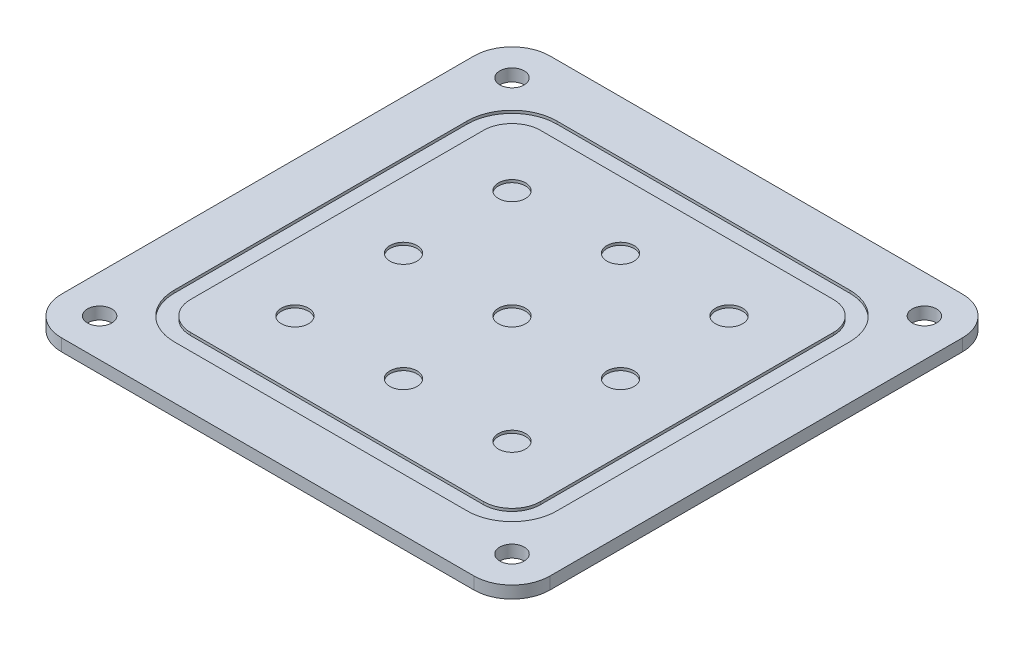
SolidWorks part; units mm, degrees
ref_plane "Front Plane" through (0, 0, 0) normal (0, 0, 1) x (1, 0, 0)
ref_plane "Top Plane" through (0, 0, 0) normal (0, 1, 0) x (1, 0, 0)
ref_plane "Right Plane" through (0, 0, 0) normal (1, 0, 0) x (0, 0, -1)
sketch "Sketch1" plane through (0, 0, 0) normal (0, 1, 0) x (1, 0, 0)
  line L1 (-45, -45) -> (45, -45)
  line L2 (-45, -45) -> (-45, 45)
  line L3 (-45, 45) -> (45, 45)
  line L4 (45, -45) -> (45, 45)
  line L5 (-45, -45) -> (45, 45) construction
  line L6 (-45, 45) -> (45, -45) construction
  point P0 (0, 0)
  dimension "D1" = 90
extrude "Boss-Extrude1" add sketch "Sketch1" along normal blind 2.25
sketch "Sketch2" plane through (0, 2.25, 0) normal (0, 1, 0) x (1, 0, 0)
  line L0 (-32.25, -27) -> (-32.25, 27)
  line L1 (-27, -35.25) -> (27, -35.25)
  line L2 (-35.25, -27) -> (-35.25, 27)
  line L3 (-27, 35.25) -> (27, 35.25)
  line L4 (35.25, -27) -> (35.25, 27)
  line L5 (0, 35.25) -> (0, -35.25) construction
  line L6 (-35.25, 0) -> (35.25, 0) construction
  line L7 (-27, 32.25) -> (27, 32.25)
  line L8 (32.25, -27) -> (32.25, 27)
  line L9 (-27, -32.25) -> (27, -32.25)
  arc A0 (-27, -35.25) -> (-35.25, -27) centre (-27, -27) cw
  arc A1 (27, -35.25) -> (35.25, -27) centre (27, -27) ccw
  arc A2 (27, 35.25) -> (35.25, 27) centre (27, 27) cw
  arc A3 (-35.25, 27) -> (-27, 35.25) centre (-27, 27) cw
  arc A4 (-32.25, 27) -> (-27, 32.25) centre (-27, 27) cw
  arc A5 (27, 32.25) -> (32.25, 27) centre (27, 27) cw
  arc A6 (27, -32.25) -> (32.25, -27) centre (27, -27) ccw
  arc A7 (-27, -32.25) -> (-32.25, -27) centre (-27, -27) cw
  circle A8 centre (-20, 20) radius 2.5
  circle A9 centre (0, 20) radius 2.5
  circle A10 centre (20, 20) radius 2.5
  circle A11 centre (0, 0) radius 2.5
  circle A12 centre (20, 0) radius 2.5
  circle A13 centre (0, -20) radius 2.5
  circle A14 centre (20, -20) radius 2.5
  circle A15 centre (-20, 0) radius 2.5
  circle A16 centre (-20, -20) radius 2.5
  point P0 (0, 0)
  point P6 (-35.25, -35.25)
  point P14 (-35.25, 35.25)
  point P30 (0, 0)
  dimension "D2" = 8.25
  dimension "D4" = 5
  dimension "D1" = 70.5
  dimension "D5" = 15.25
  dimension "D6" = 15.25
  dimension "D9" = 15.25
  dimension "D10" = 15.25
  dimension "D3" = 3
  dimension "D7" = 3
  dimension "D8" = 3
extrude "Cut-Extrude1" cut sketch "Sketch2" against normal blind 0.5 contours A3 L2 A0 L1 A1 L4 A2 L3 L9 A7 L0 A4 L7 A5 L8 A6 | A8 | A9 | A10 | A12 | A14 | A13 | A11 | A15 | A16
fillet "Fillet1" radius 7 4 edges at (-45, 1.125, -45) (45, 1.125, 45) (45, 1.125, -45) (-45, 1.125, 45)
sketch "Sketch5" plane through (0, 2.25, 0) normal (0, 1, 0) x (1, 0, 0)
  point P0 (-38, 38)
  point P3 (38, 38)
  point P6 (38, -38)
  point P9 (-38, -38)
hole_wizard "M4 Clearance Hole1" positions "Sketch5" profile "Sketch4" hole size "M4" standard "ANSI Metric" end condition through all
sketch "Sketch4" plane through (-38, 2.25, -38) normal (1, 0, 0) x (0, 0, 1)
  line L0 (0, 0) -> (0, 2.25)
  line L1 (0, 2.25) -> (2.25, 2.25)
  line L2 (2.25, 2.25) -> (2.25, 0)
  line L5 (2.25, 0) -> (0, 0)
  line L11 (0, -6.35) -> (0, 107.95) construction
  dimension "Thru Hole Dia." = 4.5
  dimension "Thru Hole Depth" = 2.25
equation "\"D5@Sketch2\"=\"D6@Sketch2\""
equation "\"D9@Sketch2\"=\"D6@Sketch2\""
equation "\"D10@Sketch2\"=\"D6@Sketch2\""
